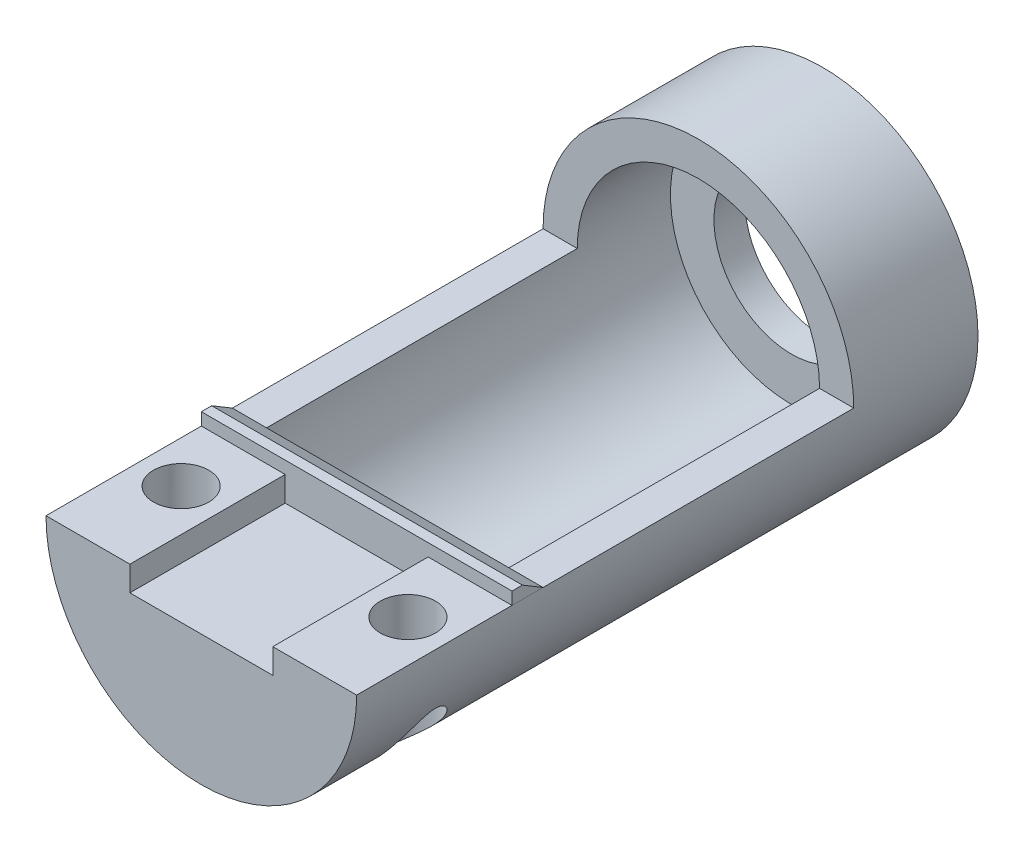
SolidWorks part; units mm, degrees
ref_plane "Front Plane" through (0, 0, 0) normal (0, 0, 1) x (1, 0, 0)
ref_plane "Top Plane" through (0, 0, 0) normal (0, 1, 0) x (1, 0, 0)
ref_plane "Right Plane" through (0, 0, 0) normal (1, 0, 0) x (0, 0, -1)
sketch "Sketch1" plane through (0, 0, 0) normal (0, 0, 1) x (1, 0, 0)
  circle A0 centre (0, 0) radius 6.35
  dimension "D1" = 12.7
extrude "Boss-Extrude1" add sketch "Sketch1" along normal mid plane 25.4
sketch "Sketch3" plane through (0, 0, 0) normal (0, 1, 0) x (1, 0, 0)
  line L0 (6.35, -12.7) -> (6.35, 12.7) construction
  line L1 (-6.35, -12.7) -> (6.35, -12.7)
  line L2 (-6.35, -12.7) -> (-6.35, 2.54)
  line L3 (-6.35, 2.54) -> (6.35, 2.54)
  line L4 (6.35, -12.7) -> (6.35, 2.54)
  dimension "D1" = 15.24
extrude "Cut-Extrude2" cut sketch "Sketch3" along normal through all
sketch "Sketch4" plane through (0, 0, -2.54) normal (0, 0, 1) x (1, 0, 0)
  line L0 (6.35, 0) -> (-6.35, 0) construction
  circle A0 centre (0, 0) radius 4.953
  dimension "D1" = 9.906
extrude "Cut-Extrude3" cut sketch "Sketch4" against normal blind 6.35 and the other way blind 6.35 from offset 2.54 offset against normal yes
sketch "Sketch5" plane through (0, 0, -11.43) normal (0, 0, 1) x (1, 0, 0)
  circle A0 centre (0, 0) radius 3.175
  dimension "D1" = 6.35
extrude "Cut-Extrude4" cut sketch "Sketch5" against normal through all
sketch "Sketch7" plane through (0, 0, 0) normal (0, 1, 0) x (1, 0, 0)
  line L0 (-6.35, -12.7) -> (6.35, -12.7) construction
  line L1 (2.921, -6.35) -> (-2.921, -6.35)
  line L2 (2.921, -6.35) -> (2.921, -12.7)
  line L3 (2.921, -12.7) -> (-2.921, -12.7)
  line L4 (-2.921, -6.35) -> (-2.921, -12.7)
  line L5 (2.921, -6.35) -> (-2.921, -12.7) construction
  line L6 (2.921, -12.7) -> (-2.921, -6.35) construction
  point P0 (0, -9.525)
  dimension "D1" = 6.35
  dimension "D2" = 5.842
extrude "Cut-Extrude5" cut sketch "Sketch7" against normal blind 1.016
sketch "Sketch8" plane through (0, 0, 0) normal (0, 1, 0) x (1, 0, 0)
  line L0 (-6.35, -12.7) -> (-2.921, -12.7) construction
  circle A0 centre (-4.6355, -8.89) radius 1.1303
  circle A1 centre (4.6355, -8.89) radius 1.1303
  dimension "D1" = 2.2606
  dimension "D2" = 3.81
extrude "Cut-Extrude6" cut sketch "Sketch8" against normal through all
sketch "Sketch9" plane through (0, 0, 0) normal (0, 1, 0) x (1, 0, 0)
  circle A0 centre (4.6355, -8.89) radius 2.413
  circle A1 centre (-4.6355, -8.89) radius 2.413
  dimension "D1" = 4.826
  dimension "D2" = 4.826
sketch "Sketch10" plane through (0, 0, -11.43) normal (0, 0, 1) x (1, 0, 0)
  circle A0 centre (0, 0) radius 4.953
extrude "Cut-Extrude7" cut sketch "Sketch10" along normal blind 16.51
sketch "Sketch11" plane through (0, 0, 5.08) normal (0, 0, -1) x (-1, 0, 0)
  line L1 (6.35, 0) -> (-6.5196, 0)
  line L2 (6.35, 0) -> (6.35, 6.5621)
  line L3 (6.35, 6.5621) -> (-6.5196, 6.5621)
  line L4 (-6.5196, 0) -> (-6.5196, 6.5621)
extrude "Cut-Extrude8" cut sketch "Sketch11" along normal blind 12.7
sketch "Sketch12" plane through (0, 0, 0) normal (1, 0, 0) x (0, 0, -1)
  line L0 (-6.35, 0) -> (-5.08, 0)
  line L1 (-5.08, 0) -> (-5.9271, 0.508)
  line L2 (-5.9271, 0.508) -> (-6.35, 0.508)
  line L3 (-6.35, 0.508) -> (-6.35, 0)
  dimension "D1" = 0.508
extrude "Boss-Extrude2" add sketch "Sketch12" along normal mid plane 12.7
